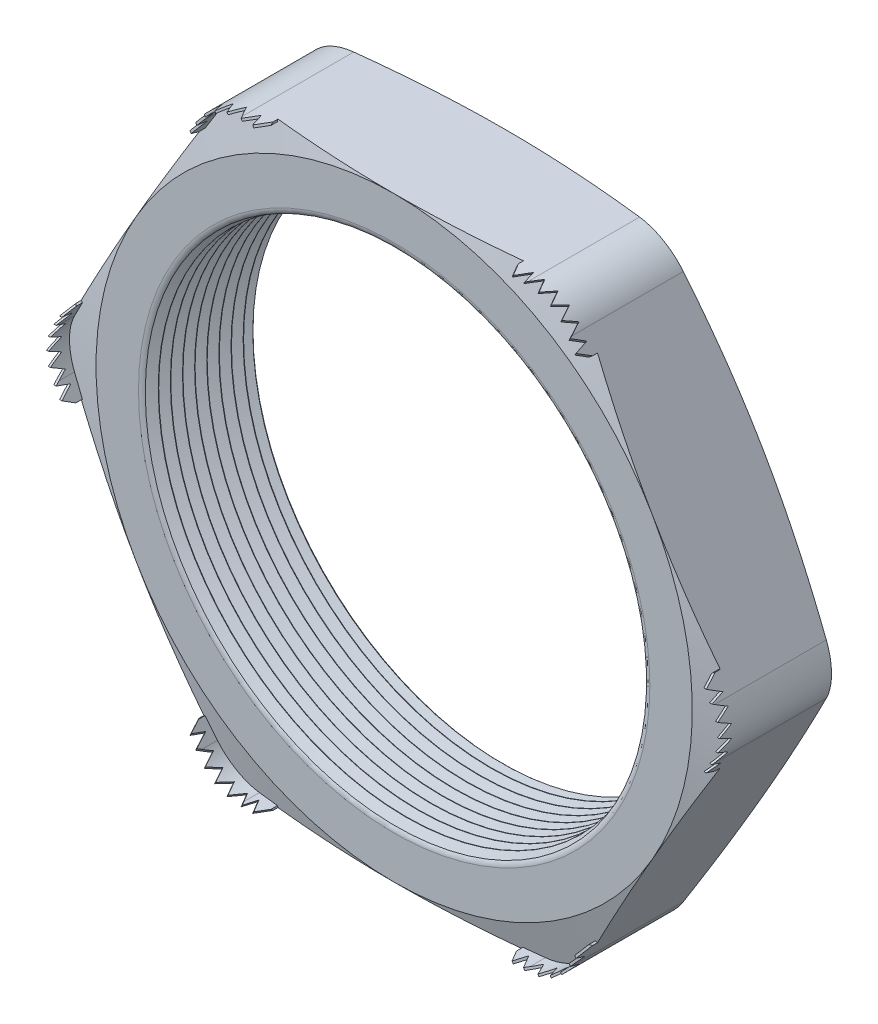
SolidWorks part; units mm, degrees
ref_plane "Front Plane" through (0, 0, 0) normal (0, 0, 1) x (1, 0, 0)
ref_plane "Top Plane" through (0, 0, 0) normal (0, 1, 0) x (1, 0, 0)
ref_plane "Right Plane" through (0, 0, 0) normal (1, 0, 0) x (0, 0, -1)
sketch "Sketch1" plane through (0, 0, 0) normal (0, 0, 1) x (1, 0, 0)
  line L1 (-8.6522, 0) -> (-4.3261, -7.493)
  line L2 (-4.3261, -7.493) -> (4.3261, -7.493)
  line L3 (4.3261, -7.493) -> (8.6522, 0)
  line L4 (8.6522, 0) -> (4.3261, 7.493)
  line L5 (4.3261, 7.493) -> (-4.3261, 7.493)
  line L6 (-4.3261, 7.493) -> (-8.6522, 0)
  circle A0 centre (0, 0) radius 7.493 construction
  circle A1 centre (0, 0) radius 6.223
  dimension "TS" = 12.446
  dimension "H" = 14.986
extrude "Extrude1" add sketch "Sketch1" along normal blind 2.794
fillet "Fillet1" radius 1.27 6 edges at (-4.3261, 7.493, 1.397) (-8.6522, 0, 1.397) (-4.3261, -7.493, 1.397) (4.3261, -7.493, 1.397) (8.6522, 0, 1.397) (4.3261, 7.493, 1.397)
sketch "Sketch2" plane through (0, 0, 2.794) normal (0, 0, 1) x (1, 0, 0)
  line L0 (-3.5929, 7.493) -> (-3.0849, 7.493)
  line L1 (3.5929, 7.493) -> (-3.5929, 7.493) construction
  line L2 (-4.6927, 6.858) -> (-4.9467, 6.4181)
  line L3 (-4.6927, 6.858) -> (-8.2856, 0.635) construction
  line L4 (-3.5929, 7.4422) -> (-3.0849, 7.4422)
  line L5 (-4.6487, 6.8326) -> (-4.9027, 6.3927)
  line L6 (-4.9467, 6.4181) -> (-4.9027, 6.3927)
  line L7 (-3.0849, 7.493) -> (-3.0849, 7.4422)
  arc A0 (-3.5929, 7.4422) -> (-4.6487, 6.8326) centre (-3.5929, 6.223) ccw
  arc A1 (-3.5929, 7.493) -> (-4.6927, 6.858) centre (-3.5929, 6.223) ccw construction
  arc A4 (-3.5929, 7.493) -> (-4.6927, 6.858) centre (-3.5929, 6.223) ccw
  dimension "D1" = 0.508
  dimension "D2" = 0.508
  dimension "OFFSET" = 0.0508
fillet "Fillet3" radius 0.2032 2 edges at (6.223, 0, 0) (6.223, 0, 2.794)
sketch "Sketch3" plane through (0, 0, 0) normal (0, 1, 0) x (1, 0, 0)
  line L0 (-6.223, -2.794) -> (-6.223, -2.5007)
  line L2 (-6.223, -2.5007) -> (-6.477, -2.6474)
  line L3 (-6.477, -2.6474) -> (-6.223, -2.794)
  line L4 (-6.223, -0.2032) -> (-6.223, -2.5908) construction
  line L5 (-4.6927, -2.794) -> (-8.2856, -2.794) construction
  dimension "D1" = 60
  dimension "D2" = 60
  dimension "D3" = 0.254
revolve "Cut-Revolve1" cut sketch "Sketch3" angle 360 about axis through (0, 0, 2.794) along (0, 0, -1)
pattern_linear "LPattern1" count 9 spacing 0.3048 along (0, 0, -1) of "Cut-Revolve1"
sketch "Sketch4" plane through (0, 0, 0) normal (0, 0, -1) x (-1, 0, 0)
  line L0 (-8.2856, 0.635) -> (-4.6927, 6.858) construction
  circle A0 centre (0, 0) radius 7.493
extrude "Cut-Extrude1" cut sketch "Sketch4" against normal through all draft 75 flip side to cut
sketch "Sketch5" plane through (0, 0, 2.794) normal (0, 0, 1) x (1, 0, 0)
  line L0 (3.5929, 7.493) -> (-3.5929, 7.493) construction
  circle A0 centre (0, 0) radius 7.493
extrude "Cut-Extrude2" cut sketch "Sketch5" against normal through all draft 75 flip side to cut
extrude "Extrude2" add sketch "Sketch2" along normal blind 0.762 and the other way up to next
ref_plane "Plane1" through (-3.9938, 6.9174, 0) normal (0.5, -0.866, 0) x (0.866, 0.5, 0)
sketch "Sketch7" plane through (-3.9938, 6.9174, 0) normal (0.5, -0.866, 0) x (0.866, 0.5, 0)
  line L0 (-1.0749, 2.7559) -> (-0.9098, 3.0759)
  line L1 (-1.0749, 2.6305) -> (-1.0749, 3.556) construction
  line L2 (0, 1.3136) -> (0, 4.0135) construction
  line L4 (-0.9098, 3.0759) -> (-0.7447, 2.7559)
  line L5 (-0.3302, 3.0759) -> (-0.1651, 2.7559)
  line L6 (-0.6604, 3.0759) -> (-0.4953, 2.7559)
  line L7 (-0.1651, 2.7559) -> (0, 3.0759)
  line L8 (0, 3.0759) -> (0.1651, 2.7559)
  line L10 (0.3302, 3.0759) -> (0.4953, 2.7559)
  line L11 (0.6604, 3.0759) -> (0.8255, 2.7559)
  line L12 (-0.7447, 2.7559) -> (-0.6604, 3.0759)
  line L13 (-0.4953, 2.7559) -> (-0.3302, 3.0759)
  line L14 (0.1651, 2.7559) -> (0.3302, 3.0759)
  line L15 (0.9098, 3.0759) -> (1.0749, 2.7559)
  line L16 (1.0749, 2.6305) -> (1.0749, 3.556) construction
  line L17 (-1.0749, 2.7559) -> (-1.0749, 3.556)
  line L19 (-1.0749, 3.556) -> (1.0749, 3.556)
  line L20 (1.0749, 3.556) -> (1.0749, 2.7559)
  line L23 (0.4953, 2.7559) -> (0.6604, 3.0759)
  line L25 (0.8255, 2.7559) -> (0.9098, 3.0759)
  dimension "D1" = 0.8001
  dimension "D2" = 0.4801
  dimension "D3" = 0.1651
extrude "Cut-Extrude4" cut sketch "Sketch7" against normal through all
pattern_circular "CirPattern1" count 6 over 360 about axis through (0, 0, 0) along (0, 0, 1) of "Extrude2"
pattern_circular "CirPattern2" count 6 over 360 about axis through (0, 0, 0) along (0, 0, 1) of "Cut-Extrude4"
